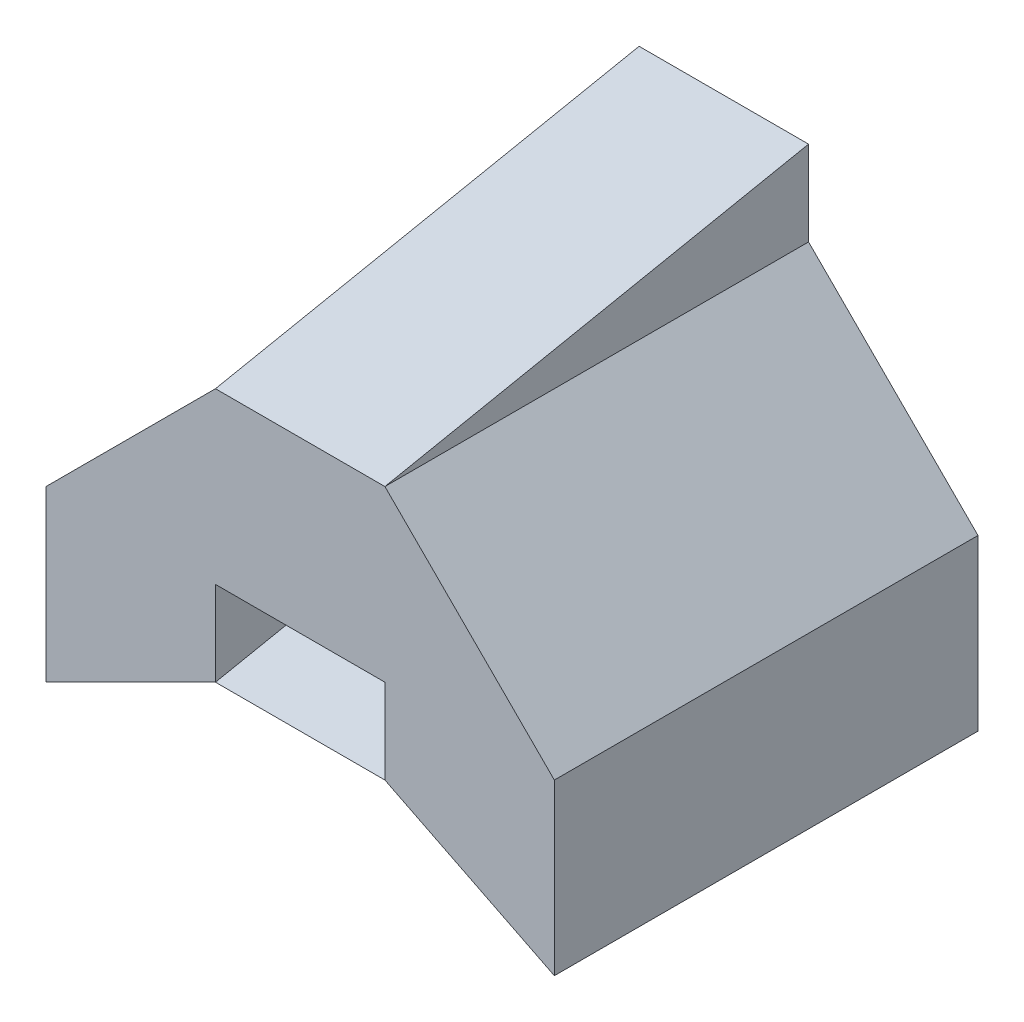
SolidWorks part; units mm, degrees
ref_plane "Front Plane" through (0, 0, 0) normal (0, 0, 1) x (1, 0, 0)
ref_plane "Top Plane" through (0, 0, 0) normal (0, 1, 0) x (1, 0, 0)
ref_plane "Right Plane" through (0, 0, 0) normal (1, 0, 0) x (0, 0, -1)
sketch "Sketch1" plane through (0, 0, 0) normal (0, 0, 1) x (1, 0, 0)
  line L0 (-10, 15) -> (-10, 20)
  line L1 (-10, 20) -> (0, 20)
  line L2 (0, 20) -> (0, 15)
  line L3 (0, 15) -> (10, 5)
  line L4 (10, 5) -> (10, -5)
  line L5 (10, -5) -> (0, 0)
  line L6 (0, 0) -> (0, 5)
  line L7 (0, 5) -> (-10, 5)
  line L8 (-10, 5) -> (-10, 0)
  line L9 (-10, 0) -> (-20, -5)
  line L10 (-20, -5) -> (-20, 5)
  line L11 (-20, 5) -> (-10, 15)
  dimension "D1" = 10
  dimension "D2" = 5
  dimension "D3" = 5
  dimension "D4" = 10
  dimension "D5" = 10
  dimension "D6" = 10
  dimension "D7" = 10
  dimension "D8" = 5
  dimension "D9" = 5
  dimension "D10" = 10
  dimension "D11" = 10
  dimension "D12" = 10
  dimension "D13" = 10
  dimension "D14" = 5
extrude "Boss-Extrude1" add sketch "Sketch1" along normal blind 25
sketch "Sketch2" plane through (0, 0, 0) normal (1, 0, 0) x (0, 0, -1)
  line L0 (-25, 15) -> (0, 20)
  line L1 (0, 20) -> (-25, 20)
  line L2 (-25, 20) -> (-25, 15)
extrude "Cut-Extrude1" cut sketch "Sketch2" against normal blind 25
sketch "Sketch3" plane through (-10, 0, 0) normal (1, 0, 0) x (0, 0, -1)
  line L0 (-25, 0) -> (0, 5)
  line L1 (0, 5) -> (0, 0)
  line L2 (0, 0) -> (-25, 0)
extrude "Boss-Extrude3" add sketch "Sketch3" along normal blind 10 separate body
